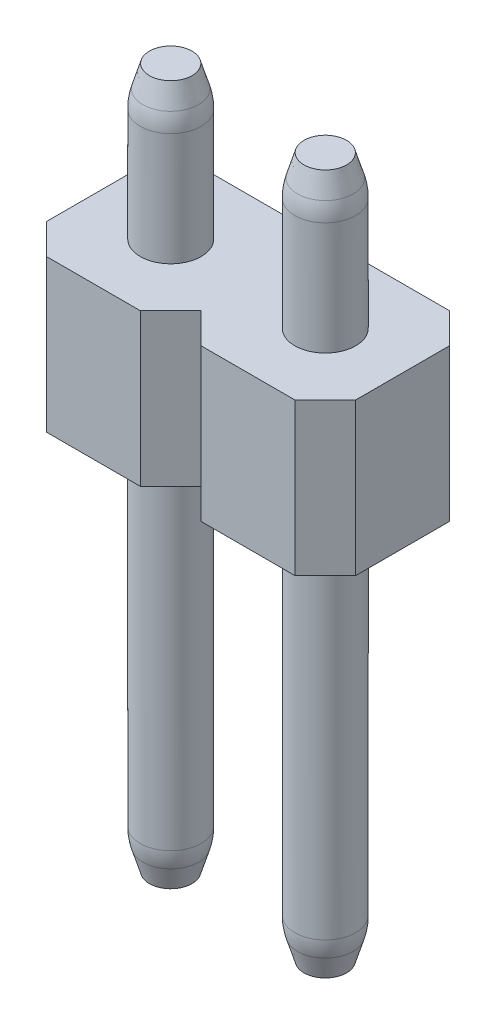
SolidWorks part; units mm, degrees
material "Brass"
ref_plane "Front Plane" through (0, 0, 0) normal (0, 0, 1) x (1, 0, 0)
ref_plane "Top Plane" through (0, 0, 0) normal (0, 1, 0) x (1, 0, 0)
ref_plane "Right Plane" through (0, 0, 0) normal (1, 0, 0) x (0, 0, -1)
sketch "Sketch1" plane through (0, 0, 0) normal (0, 1, 0) x (1, 0, 0)
  line L0 (0, 0) -> (2.54, 0) construction
  circle A0 centre (0, 0) radius 0.5
  circle A1 centre (2.54, 0) radius 0.5
  circle A2 centre (5.08, 0) radius 0.5
  circle A3 centre (7.62, 0) radius 0.5
  circle A4 centre (10.16, 0) radius 0.5
  circle A5 centre (12.7, 0) radius 0.5
  circle A6 centre (15.24, 0) radius 0.5
  circle A7 centre (17.78, 0) radius 0.5
  circle A8 centre (20.32, 0) radius 0.5
  circle A9 centre (22.86, 0) radius 0.5
  circle A10 centre (25.4, 0) radius 0.5
  circle A11 centre (27.94, 0) radius 0.5
  circle A12 centre (30.48, 0) radius 0.5
  circle A13 centre (33.02, 0) radius 0.5
  circle A14 centre (35.56, 0) radius 0.5
  circle A15 centre (38.1, 0) radius 0.5
  dimension "D1" = 1
  dimension "D3" = 2.54
  dimension "D2" = 16
extrude "Boss-Extrude1" add sketch "Sketch1" along normal blind 11.5
ref_plane "Plane1" through (0, 6.5, 0) normal (0, 1, 0) x (1, 0, 0)
sketch "Sketch2" plane through (0, 6.5, 0) normal (0, 1, 0) x (1, 0, 0)
  line L0 (-1.27, 0.77) -> (-0.77, 1.27)
  line L1 (-0.77, -1.27) -> (0.77, -1.27)
  line L2 (-1.27, -0.77) -> (-1.27, 0.77)
  line L3 (-0.77, 1.27) -> (0.77, 1.27)
  line L5 (-1.27, -1.27) -> (1.27, 1.27) construction
  line L6 (-1.27, 1.27) -> (1.27, -1.27) construction
  line L7 (0.77, 1.27) -> (1.27, 0.77)
  line L8 (0.77, -1.27) -> (1.27, -0.77)
  line L9 (-1.27, -0.77) -> (-0.77, -1.27)
  line L10 (1.27, 0.77) -> (1.77, 1.27)
  line L11 (1.77, 1.27) -> (3.31, 1.27)
  line L12 (3.31, 1.27) -> (3.81, 0.77)
  line L14 (3.31, -1.27) -> (3.81, -0.77)
  line L15 (1.77, -1.27) -> (3.31, -1.27)
  line L16 (1.27, -0.77) -> (1.77, -1.27)
  line L17 (3.81, 0.77) -> (4.31, 1.27)
  line L18 (4.31, 1.27) -> (5.85, 1.27)
  line L19 (5.85, 1.27) -> (6.35, 0.77)
  line L20 (6.35, -0.77) -> (6.35, 0.77) construction
  line L21 (5.85, -1.27) -> (6.35, -0.77)
  line L22 (4.31, -1.27) -> (5.85, -1.27)
  line L23 (3.81, -0.77) -> (4.31, -1.27)
  line L24 (6.35, 0.77) -> (6.85, 1.27)
  line L25 (6.85, 1.27) -> (8.39, 1.27)
  line L26 (8.39, 1.27) -> (8.89, 0.77)
  line L27 (8.89, -0.77) -> (8.89, 0.77) construction
  line L28 (8.39, -1.27) -> (8.89, -0.77)
  line L29 (6.85, -1.27) -> (8.39, -1.27)
  line L30 (6.35, -0.77) -> (6.85, -1.27)
  line L31 (8.89, 0.77) -> (9.39, 1.27)
  line L32 (9.39, 1.27) -> (10.93, 1.27)
  line L33 (10.93, 1.27) -> (11.43, 0.77)
  line L34 (11.43, -0.77) -> (11.43, 0.77) construction
  line L35 (10.93, -1.27) -> (11.43, -0.77)
  line L36 (9.39, -1.27) -> (10.93, -1.27)
  line L37 (8.89, -0.77) -> (9.39, -1.27)
  line L38 (11.43, 0.77) -> (11.93, 1.27)
  line L39 (11.93, 1.27) -> (13.47, 1.27)
  line L40 (13.47, 1.27) -> (13.97, 0.77)
  line L41 (13.97, -0.77) -> (13.97, 0.77) construction
  line L42 (13.47, -1.27) -> (13.97, -0.77)
  line L43 (11.93, -1.27) -> (13.47, -1.27)
  line L44 (11.43, -0.77) -> (11.93, -1.27)
  line L45 (13.97, 0.77) -> (14.47, 1.27)
  line L46 (14.47, 1.27) -> (16.01, 1.27)
  line L47 (16.01, 1.27) -> (16.51, 0.77)
  line L48 (16.51, -0.77) -> (16.51, 0.77) construction
  line L49 (16.01, -1.27) -> (16.51, -0.77)
  line L50 (14.47, -1.27) -> (16.01, -1.27)
  line L51 (13.97, -0.77) -> (14.47, -1.27)
  line L52 (16.51, 0.77) -> (17.01, 1.27)
  line L53 (17.01, 1.27) -> (18.55, 1.27)
  line L54 (18.55, 1.27) -> (19.05, 0.77)
  line L55 (19.05, -0.77) -> (19.05, 0.77) construction
  line L56 (18.55, -1.27) -> (19.05, -0.77)
  line L57 (17.01, -1.27) -> (18.55, -1.27)
  line L58 (16.51, -0.77) -> (17.01, -1.27)
  line L59 (19.05, 0.77) -> (19.55, 1.27)
  line L60 (19.55, 1.27) -> (21.09, 1.27)
  line L61 (21.09, 1.27) -> (21.59, 0.77)
  line L62 (21.59, -0.77) -> (21.59, 0.77) construction
  line L63 (21.09, -1.27) -> (21.59, -0.77)
  line L64 (19.55, -1.27) -> (21.09, -1.27)
  line L65 (19.05, -0.77) -> (19.55, -1.27)
  line L66 (21.59, 0.77) -> (22.09, 1.27)
  line L67 (22.09, 1.27) -> (23.63, 1.27)
  line L68 (23.63, 1.27) -> (24.13, 0.77)
  line L69 (24.13, -0.77) -> (24.13, 0.77) construction
  line L70 (23.63, -1.27) -> (24.13, -0.77)
  line L71 (22.09, -1.27) -> (23.63, -1.27)
  line L72 (21.59, -0.77) -> (22.09, -1.27)
  line L73 (24.13, 0.77) -> (24.63, 1.27)
  line L74 (24.63, 1.27) -> (26.17, 1.27)
  line L75 (26.17, 1.27) -> (26.67, 0.77)
  line L76 (26.67, -0.77) -> (26.67, 0.77) construction
  line L77 (26.17, -1.27) -> (26.67, -0.77)
  line L78 (24.63, -1.27) -> (26.17, -1.27)
  line L79 (24.13, -0.77) -> (24.63, -1.27)
  line L80 (26.67, 0.77) -> (27.17, 1.27)
  line L81 (27.17, 1.27) -> (28.71, 1.27)
  line L82 (28.71, 1.27) -> (29.21, 0.77)
  line L83 (29.21, -0.77) -> (29.21, 0.77) construction
  line L84 (28.71, -1.27) -> (29.21, -0.77)
  line L85 (27.17, -1.27) -> (28.71, -1.27)
  line L86 (26.67, -0.77) -> (27.17, -1.27)
  line L87 (29.21, 0.77) -> (29.71, 1.27)
  line L88 (29.71, 1.27) -> (31.25, 1.27)
  line L89 (31.25, 1.27) -> (31.75, 0.77)
  line L90 (31.75, -0.77) -> (31.75, 0.77) construction
  line L91 (31.25, -1.27) -> (31.75, -0.77)
  line L92 (29.71, -1.27) -> (31.25, -1.27)
  line L93 (29.21, -0.77) -> (29.71, -1.27)
  line L94 (31.75, 0.77) -> (32.25, 1.27)
  line L95 (32.25, 1.27) -> (33.79, 1.27)
  line L96 (33.79, 1.27) -> (34.29, 0.77)
  line L97 (34.29, -0.77) -> (34.29, 0.77) construction
  line L98 (33.79, -1.27) -> (34.29, -0.77)
  line L99 (32.25, -1.27) -> (33.79, -1.27)
  line L100 (31.75, -0.77) -> (32.25, -1.27)
  line L101 (34.29, 0.77) -> (34.79, 1.27)
  line L102 (34.79, 1.27) -> (36.33, 1.27)
  line L103 (36.33, 1.27) -> (36.83, 0.77)
  line L104 (36.83, -0.77) -> (36.83, 0.77) construction
  line L105 (36.33, -1.27) -> (36.83, -0.77)
  line L106 (34.79, -1.27) -> (36.33, -1.27)
  line L107 (34.29, -0.77) -> (34.79, -1.27)
  line L108 (36.83, 0.77) -> (37.33, 1.27)
  line L109 (37.33, 1.27) -> (38.87, 1.27)
  line L110 (38.87, 1.27) -> (39.37, 0.77)
  line L111 (39.37, -0.77) -> (39.37, 0.77)
  line L112 (38.87, -1.27) -> (39.37, -0.77)
  line L113 (37.33, -1.27) -> (38.87, -1.27)
  line L114 (36.83, -0.77) -> (37.33, -1.27)
  line L115 (-1.27, 0.77) -> (1.27, 0.77) construction
  point P0 (0, 0)
  dimension "D1" = 2.54
  dimension "D2" = 2.54
  dimension "D4" = 2.54
  dimension "D3" = 16
extrude "Boss-Extrude2" add sketch "Sketch2" along normal blind 2.5
chamfer "Chamfer1" distance 0.5 distance2 0.15 16 edges at (15.24, 11.5, 0.5) (12.7, 11.5, 0.5) (10.16, 11.5, 0.5) (7.62, 11.5, 0.5) (5.08, 11.5, 0.5) (2.54, 11.5, 0.5) (0, 11.5, 0.5) (38.1, 11.5, 0.5) (35.56, 11.5, 0.5) (33.02, 11.5, 0.5) (30.48, 11.5, 0.5) (27.94, 11.5, 0.5) (25.4, 11.5, 0.5) (22.86, 11.5, 0.5) (20.32, 11.5, 0.5) (17.78, 11.5, 0.5)
fillet "Fillet1" radius 1 16 edges at (38.1, 11, 0.5) (35.56, 11, 0.5) (33.02, 11, 0.5) (30.48, 11, 0.5) (27.94, 11, 0.5) (25.4, 11, 0.5) (22.86, 11, 0.5) (20.32, 11, 0.5) (17.78, 11, 0.5) (15.24, 11, 0.5) (12.7, 11, 0.5) (10.16, 11, 0.5) (7.62, 11, 0.5) (5.08, 11, 0.5) (2.54, 11, 0.5) (0, 11, 0.5)
chamfer "Chamfer2" distance 0.15 distance2 0.5 16 edges at (10.16, 0, 0.5) (17.78, 0, 0.5) (22.86, 0, 0.5) (27.94, 0, 0.5) (30.48, 0, 0.5) (0, 0, 0.5) (2.54, 0, 0.5) (5.08, 0, 0.5) (7.62, 0, 0.5) (12.7, 0, 0.5) (15.24, 0, 0.5) (20.32, 0, 0.5) (25.4, 0, 0.5) (33.02, 0, 0.5) (35.56, 0, 0.5) (38.1, 0, 0.5)
fillet "Fillet2" radius 1 16 edges at (30.48, 0.5, 0.5) (33.02, 0.5, 0.5) (35.56, 0.5, 0.5) (38.1, 0.5, 0.5) (27.94, 0.5, 0.5) (25.4, 0.5, 0.5) (22.86, 0.5, 0.5) (20.32, 0.5, 0.5) (17.78, 0.5, 0.5) (15.24, 0.5, 0.5) (12.7, 0.5, 0.5) (10.16, 0.5, 0.5) (7.62, 0.5, 0.5) (5.08, 0.5, 0.5) (2.54, 0.5, 0.5) (0, 0.5, 0.5)
sketch "Sketch3" plane through (0, 0, 1.27) normal (0, 0, 1) x (1, 0, 0)
  line L0 (29.21, 9) -> (29.21, 6.5) construction
  line L1 (29.21, 9) -> (29.21, 6.5)
  line L2 (29.21, 9) -> (29.21, 12.0063)
  line L3 (29.21, 12.0063) -> (41.7324, 12.0063)
  line L4 (41.7324, 12.0063) -> (41.7324, -0.9046)
  line L5 (41.7324, -0.9046) -> (29.21, -0.9046)
  line L6 (29.21, -0.9046) -> (29.21, 6.5)
extrude "Cut-Extrude1" cut sketch "Sketch3" against normal through all
sketch "Sketch4" plane through (0, 0, 1.27) normal (0, 0, 1) x (1, 0, 0)
  line L0 (16.51, 9) -> (16.51, 6.5) construction
  line L1 (16.51, 9) -> (16.51, 6.5)
  line L2 (16.51, 9) -> (16.51, 12.1306)
  line L3 (16.51, 12.1306) -> (30.5961, 12.1306)
  line L4 (30.5961, 12.1306) -> (30.5961, -1.1631)
  line L5 (30.5961, -1.1631) -> (16.51, -1.1631)
  line L6 (16.51, -1.1631) -> (16.51, 6.5)
extrude "Cut-Extrude2" cut sketch "Sketch4" against normal through all
sketch "Sketch5" plane through (0, 0, 1.27) normal (0, 0, 1) x (1, 0, 0)
  line L0 (3.81, 9) -> (3.81, 6.5) construction
  line L1 (3.81, 11.5) -> (3.81, 0)
  line L2 (3.81, 11.5) -> (16.51, 11.5)
  line L3 (16.51, 11.5) -> (16.51, 0)
  line L4 (16.51, 0) -> (3.81, 0)
extrude "Cut-Extrude3" cut sketch "Sketch5" against normal through all both and the other way through all
